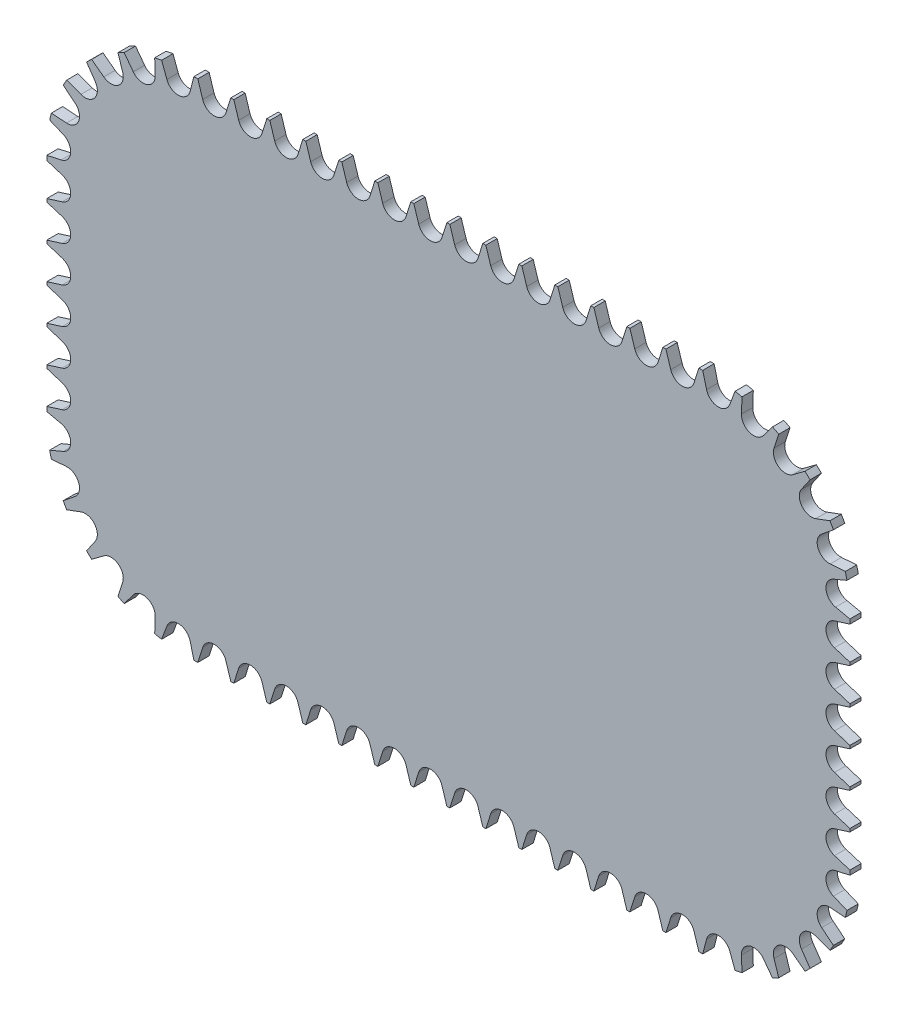
SolidWorks part; units mm, degrees
ref_plane "Ebene vorne" through (0, 0, 0) normal (0, 0, 1) x (1, 0, 0)
ref_plane "Ebene oben" through (0, 0, 0) normal (0, 1, 0) x (1, 0, 0)
ref_plane "Ebene rechts" through (0, 0, 0) normal (1, 0, 0) x (0, 0, -1)
sketch "Skizze1" plane through (0, 0, 0) normal (0, 0, 1) x (1, 0, 0)
  line L1 (-92.5, -90) -> (92.5, -90)
  line L2 (-142.5, -40) -> (-142.5, 40)
  line L3 (-92.5, 90) -> (92.5, 90)
  line L4 (142.5, -40) -> (142.5, 40)
  line L5 (-142.5, -90) -> (142.5, 90) construction
  line L6 (-142.5, 90) -> (142.5, -90) construction
  arc A0 (-92.5, -90) -> (-142.5, -40) centre (-92.5, -40) cw
  arc A1 (92.5, -90) -> (142.5, -40) centre (92.5, -40) ccw
  arc A2 (92.5, 90) -> (142.5, 40) centre (92.5, 40) cw
  arc A3 (-142.5, 40) -> (-92.5, 90) centre (-92.5, 40) cw
  point P0 (0, 0)
  dimension "D3" = 50
  dimension "D1" = 285
  dimension "D2" = 180
extrude "Aufsatz-Linear austragen1" add sketch "Skizze1" along normal blind 4
sketch "Skizze2" plane through (0, 0, 4) normal (0, 0, 1) x (1, 0, 0)
  line L0 (0, 0) -> (0, 110.2659) construction
  line L1 (0, 0) -> (-156.33, 0) construction
  line L2 (0, 85) -> (-92.9233, 85)
  line L3 (-137.5, 40.4233) -> (-137.5, 0)
  line L4 (-142.5, -40) -> (-142.5, 40) construction
  line L5 (-92.5, 90) -> (92.5, 90) construction
  arc A0 (-92.9233, 85) -> (-137.5, 40.4233) centre (-92.9233, 40.4233) ccw
  circle A1 centre (-6.35, 85) radius 6.35
  circle A2 centre (-19.05, 85) radius 6.35
  circle A3 centre (-31.75, 85) radius 6.35
  circle A4 centre (-44.45, 85) radius 6.35
  circle A5 centre (-57.15, 85) radius 6.35
  circle A6 centre (-69.85, 85) radius 6.35
  circle A7 centre (-82.55, 85) radius 6.35
  circle A8 centre (-95.25, 85) radius 6.35
  circle A9 centre (-107.6976, 82.4804) radius 6.35
  circle A10 centre (-118.9579, 76.6073) radius 6.35
  circle A11 centre (-128.1051, 67.7971) radius 6.35
  circle A12 centre (-134.3966, 56.765) radius 6.35
  circle A13 centre (-137.5, 44.45) radius 6.35
  circle A14 centre (-137.5, 31.75) radius 6.35
  circle A15 centre (-137.5, 19.05) radius 6.35
  circle A16 centre (-137.5, 6.35) radius 6.35
  circle A17 centre (-137.5, 19.05) radius 6.35
  circle A18 centre (-137.5, 31.75) radius 6.35
  dimension "D1" = 12.7
  dimension "D2" = 5
  dimension "D3" = 5
sketch "Skizze3" plane through (0, 0, 4) normal (0, 0, 1) x (1, 0, 0)
  line L0 (-137.5, 44.45) -> (-136.2122, 44.3337) construction
  line L1 (-137.1801, 45.9743) -> (-137.3192, 44.4337) construction
  line L2 (-95.2468, 84.9394) -> (-95.25, 85) construction
  line L3 (-92.5677, 85.0792) -> (-95.2468, 84.9394) construction
  line L4 (-137.5, 40.4233) -> (-137.5, 0) construction
  line L6 (-2.249, 83.707) -> (-2.2971, 83.2603) construction
  arc A1 (-92.9233, 85) -> (-137.5, 40.4233) centre (-92.9233, 40.4233) ccw construction
  line B0 (-12.4982, 90.2) -> (-10.451, 83.707)
  line B1 (-2.249, 83.707) -> (-0.2018, 90.2)
  line B2 (-0.2018, 90.2) -> (-12.4982, 90.2)
  line B3 (-6.35, 85) -> (-6.35, 90.2) construction
  line B4 (-10.451, 83.707) -> (-2.249, 83.707) construction
  line B5 (-6.35, 85) -> (3.1789, 85) construction
  arc B6 (-10.451, 83.707) -> (-2.249, 83.707) centre (-6.35, 85) ccw
  line B7 (-115.2217, 85.3488) -> (-111.1382, 79.9013)
  line B8 (-103.3998, 82.6197) -> (-103.6203, 89.4243)
  line B9 (-103.6203, 89.4243) -> (-115.2217, 85.3488)
  arc B10 (-111.1382, 79.9013) -> (-103.3998, 82.6197) centre (-107.6976, 82.4804) ccw
  line B11 (-101.6609, 89.8725) -> (-99.278, 83.495)
  line B12 (-91.0872, 83.9225) -> (-89.3812, 90.5134)
  line B13 (-89.3812, 90.5134) -> (-101.6609, 89.8725)
  line B14 (-95.25, 85) -> (-95.521, 90.1929) construction
  arc B15 (-99.278, 83.495) -> (-91.0872, 83.9225) centre (-95.25, 85) ccw
  line B16 (-126.9856, 77.2374) -> (-121.5316, 73.1625)
  line B17 (-114.8739, 77.9528) -> (-117.0043, 84.4191)
  line B18 (-117.0043, 84.4191) -> (-126.9856, 77.2374)
  line B19 (-121.5316, 73.1625) -> (-114.8739, 77.9528) construction
  arc B20 (-121.5316, 73.1625) -> (-114.8739, 77.9528) centre (-118.9579, 76.6073) ccw
  line B21 (-135.9847, 66.1379) -> (-129.6029, 63.7664)
  line B22 (-124.5662, 70.2397) -> (-128.4336, 75.8428)
  line B23 (-128.4336, 75.8428) -> (-135.9847, 66.1379)
  line B24 (-128.1051, 67.7971) -> (-132.2091, 70.9903) construction
  line B25 (-129.6029, 63.7664) -> (-124.5662, 70.2397) construction
  arc B26 (-129.6029, 63.7664) -> (-124.5662, 70.2397) centre (-128.1051, 67.7971) ccw
  line B27 (-141.4885, 52.9511) -> (-134.697, 52.4755)
  line B28 (-131.6901, 60.1064) -> (-136.9806, 64.3915)
  line B29 (-136.9806, 64.3915) -> (-141.4885, 52.9511)
  arc B30 (-134.697, 52.4755) -> (-131.6901, 60.1064) centre (-134.3966, 56.765) ccw
  line B31 (-143.232, 38.7945) -> (-136.5812, 40.2493)
  line B32 (-135.8433, 48.418) -> (-142.1258, 51.0411)
  line B33 (-142.1258, 51.0411) -> (-143.232, 38.7945)
  arc B34 (-136.5812, 40.2493) -> (-135.8433, 48.418) centre (-137.5, 44.45) ccw
  line B35 (-142.7, 25.6018) -> (-136.207, 27.649)
  line B36 (-136.207, 35.851) -> (-142.7, 37.8982)
  line B37 (-142.7, 37.8982) -> (-142.7, 25.6018)
  arc B38 (-136.207, 27.649) -> (-136.207, 35.851) centre (-137.5, 31.75) ccw
  line B39 (-142.7, 12.9018) -> (-136.207, 14.949)
  line B40 (-136.207, 23.151) -> (-142.7, 25.1982)
  line B41 (-142.7, 25.1982) -> (-142.7, 12.9018)
  arc B42 (-136.207, 14.949) -> (-136.207, 23.151) centre (-137.5, 19.05) ccw
  line B43 (-142.7, 0.2018) -> (-136.207, 2.249)
  line B44 (-136.207, 10.451) -> (-142.7, 12.4982)
  line B45 (-142.7, 12.4982) -> (-142.7, 0.2018)
  arc B46 (-136.207, 2.249) -> (-136.207, 10.451) centre (-137.5, 6.35) ccw
  line B47 (-25.1982, 90.2) -> (-23.151, 83.707)
  line B48 (-14.949, 83.707) -> (-12.9018, 90.2)
  line B49 (-12.9018, 90.2) -> (-25.1982, 90.2)
  arc B50 (-23.151, 83.707) -> (-14.949, 83.707) centre (-19.05, 85) ccw
  line B51 (-37.8982, 90.2) -> (-35.851, 83.707)
  line B52 (-27.649, 83.707) -> (-25.6018, 90.2)
  line B53 (-25.6018, 90.2) -> (-37.8982, 90.2)
  arc B54 (-35.851, 83.707) -> (-27.649, 83.707) centre (-31.75, 85) ccw
  line B55 (-50.5982, 90.2) -> (-48.551, 83.707)
  line B56 (-40.349, 83.707) -> (-38.3018, 90.2)
  line B57 (-38.3018, 90.2) -> (-50.5982, 90.2)
  arc B58 (-48.551, 83.707) -> (-40.349, 83.707) centre (-44.45, 85) ccw
  line B59 (-63.2982, 90.2) -> (-61.251, 83.707)
  line B60 (-53.049, 83.707) -> (-51.0018, 90.2)
  line B61 (-51.0018, 90.2) -> (-63.2982, 90.2)
  arc B62 (-61.251, 83.707) -> (-53.049, 83.707) centre (-57.15, 85) ccw
  line B63 (-75.9982, 90.2) -> (-73.951, 83.707)
  line B64 (-65.749, 83.707) -> (-63.7018, 90.2)
  line B65 (-63.7018, 90.2) -> (-75.9982, 90.2)
  arc B66 (-73.951, 83.707) -> (-65.749, 83.707) centre (-69.85, 85) ccw
  line B67 (-88.6982, 90.2) -> (-86.651, 83.707)
  line B68 (-78.449, 83.707) -> (-76.4018, 90.2)
  line B69 (-76.4018, 90.2) -> (-88.6982, 90.2)
  arc B70 (-86.651, 83.707) -> (-78.449, 83.707) centre (-82.55, 85) ccw
  dimension "D1" = 7
sketch_block_instance "Block1-1"
sketch_block "Block1" parameters "D1"=4.3, "D2"=5.2, "D3"=35
sketch_block_instance "Block1-2"
sketch_block_instance "Block1-3"
sketch_block_instance "Block1-4"
sketch_block_instance "Block1-5"
sketch_block_instance "Block1-6"
sketch_block_instance "Block1-7"
sketch_block_instance "Block1-8"
sketch_block_instance "Block1-9"
sketch_block_instance "Block1-10"
sketch_block_instance "Block1-11"
sketch_block_instance "Block1-12"
sketch_block_instance "Block1-13"
sketch_block_instance "Block1-14"
sketch_block_instance "Block1-15"
sketch_block_instance "Block1-16"
extrude "Schnitt-Linear austragen1" cut sketch "Skizze3" against normal through all
mirror "Spiegeln1" about plane through (0, 0, 0) normal (0, 1, 0) of "Schnitt-Linear austragen1"
mirror "Spiegeln2" about plane through (0, 0, 0) normal (1, 0, 0) of "Spiegeln1", "Schnitt-Linear austragen1"
sketch "Skizze4" plane through (0, 0, 4) normal (0, 0, 1) x (1, 0, 0)
  line L0 (0, 85) -> (-92.9233, 85) construction
  line L1 (92.92, -89.14) -> (-92.92, -89.14)
  line L2 (141.64, -40.42) -> (141.64, 40.42)
  line L3 (92.92, 89.14) -> (-92.92, 89.14)
  line L4 (-141.64, -40.42) -> (-141.64, 40.42)
  line L5 (141.64, -89.14) -> (-141.64, 89.14) construction
  line L6 (141.64, 89.14) -> (-141.64, -89.14) construction
  line L7 (-137.5, 40.4233) -> (-137.5, 0) construction
  arc A2 (-92.92, -89.14) -> (-141.64, -40.42) centre (-92.92, -40.42) cw
  arc A3 (92.92, -89.14) -> (141.64, -40.42) centre (92.92, -40.42) ccw
  arc A4 (141.64, 40.42) -> (92.92, 89.14) centre (92.92, 40.42) ccw
  arc A5 (-92.92, 89.14) -> (-141.64, 40.42) centre (-92.92, 40.42) ccw
  point P0 (0, 0)
  dimension "D3" = 48.72
  dimension "D1" = 4.14
  dimension "D2" = 4.14
extrude "Schnitt-Linear austragen2" cut sketch "Skizze4" against normal through all flip side to cut
